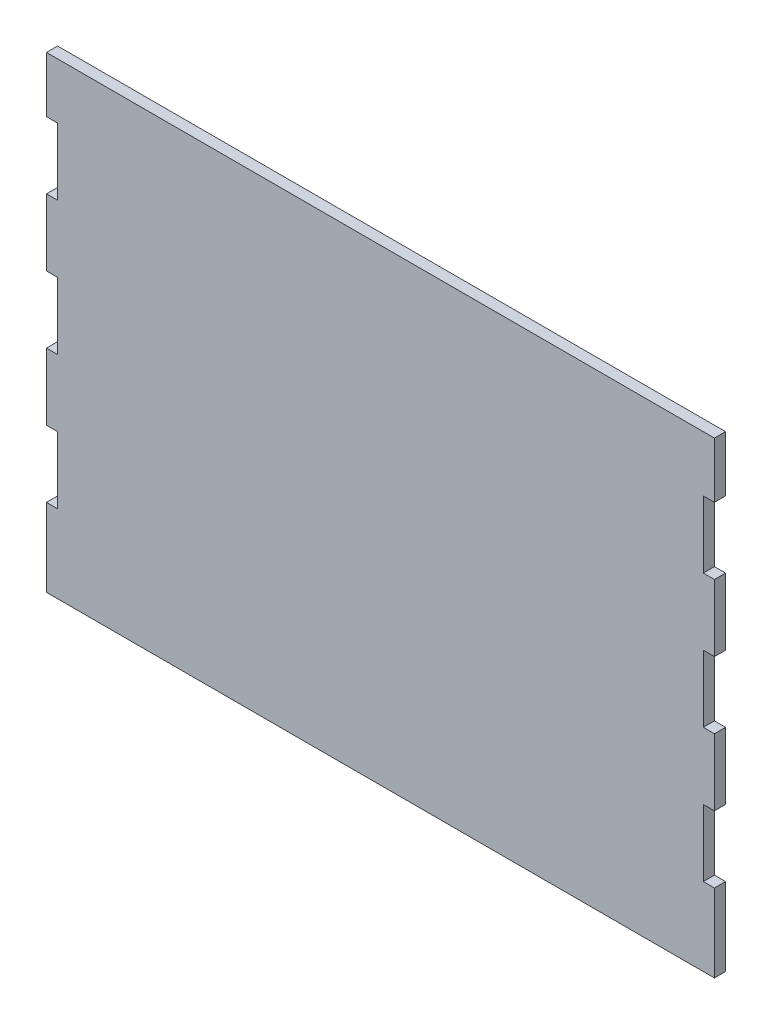
SolidWorks part; units mm, degrees
ref_plane "Front Plane" through (0, 0, 0) normal (0, 0, 1) x (1, 0, 0)
ref_plane "Top Plane" through (0, 0, 0) normal (0, 1, 0) x (1, 0, 0)
ref_plane "Right Plane" through (0, 0, 0) normal (1, 0, 0) x (0, 0, -1)
sketch "Sketch1" plane through (0, 0, 0) normal (0, 0, 1) x (1, 0, 0)
  line L1 (-150, 105) -> (150, 105)
  line L2 (-150, 105) -> (-150, -105)
  line L3 (-150, -105) -> (150, -105)
  line L4 (150, 105) -> (150, -105)
  line L5 (-150, 105) -> (150, -105) construction
  line L6 (-150, -105) -> (150, 105) construction
  point P0 (0, 0)
  dimension "D1" = 300
  dimension "D2" = 210
extrude "Boss-Extrude1" add sketch "Sketch1" along normal blind 5
sketch "Sketch2" plane through (0, 0, 0) normal (0, 0, -1) x (-1, 0, 0)
  line L0 (-150, 105) -> (150, 105) construction
  line L1 (-212.6198, 80) -> (-145, 80)
  line L2 (-212.6198, 80) -> (-212.6198, 50)
  line L3 (-212.6198, 50) -> (-145, 50)
  line L4 (-145, 80) -> (-145, 50)
  line L5 (-212.6198, 80) -> (-145, 50) construction
  line L6 (-212.6198, 50) -> (-145, 80) construction
  line L7 (-150, -105) -> (-150, 105) construction
  line L8 (-217.6198, 20) -> (-145, 20)
  line L9 (-217.6198, 20) -> (-217.6198, -10)
  line L10 (-217.6198, -10) -> (-145, -10)
  line L11 (-145, 20) -> (-145, -10)
  line L12 (-217.6198, 20) -> (-145, -10) construction
  line L13 (-217.6198, -10) -> (-145, 20) construction
  line L14 (-217.6198, -70) -> (-145, -70)
  line L15 (-217.6198, -70) -> (-217.6198, -40)
  line L16 (-217.6198, -40) -> (-145, -40)
  line L17 (-145, -70) -> (-145, -40)
  line L18 (-217.6198, -70) -> (-145, -40) construction
  line L19 (-217.6198, -40) -> (-145, -70) construction
  line L21 (145, 80) -> (198.2126, 80)
  line L22 (145, 80) -> (145, 50)
  line L23 (145, 50) -> (198.2126, 50)
  line L24 (198.2126, 80) -> (198.2126, 50)
  line L25 (145, 80) -> (198.2126, 50) construction
  line L26 (145, 50) -> (198.2126, 80) construction
  line L27 (145, 20) -> (217.6198, 20)
  line L28 (145, 20) -> (145, -10)
  line L29 (145, -10) -> (217.6198, -10)
  line L30 (217.6198, 20) -> (217.6198, -10)
  line L31 (145, 20) -> (217.6198, -10) construction
  line L32 (145, -10) -> (217.6198, 20) construction
  line L33 (145, -70) -> (217.6198, -70)
  line L34 (145, -70) -> (145, -40)
  line L35 (145, -40) -> (217.6198, -40)
  line L36 (217.6198, -70) -> (217.6198, -40)
  line L37 (145, -70) -> (217.6198, -40) construction
  line L38 (145, -40) -> (217.6198, -70) construction
  line L40 (150, 105) -> (150, -105) construction
  point P0 (-178.8099, 65)
  point P9 (-181.3099, 5)
  point P14 (-181.3099, -55)
  point P22 (171.6063, 65)
  point P27 (181.3099, 5)
  point P32 (181.3099, -55)
  dimension "D1" = 25
  dimension "D2" = 5
  dimension "D3" = 30
  dimension "D4" = 30
  dimension "D5" = 30
  dimension "D6" = 5
  dimension "D7" = 30
  dimension "D8" = 30
  dimension "D9" = 5
  dimension "D10" = 30
  dimension "D11" = 30
  dimension "D12" = 30
  dimension "D13" = 25
  dimension "D14" = 30
  dimension "D15" = 30
  dimension "D16" = 5
  dimension "D17" = 5
  dimension "D18" = 5
extrude "Cut-Extrude1" cut sketch "Sketch2" against normal through all
